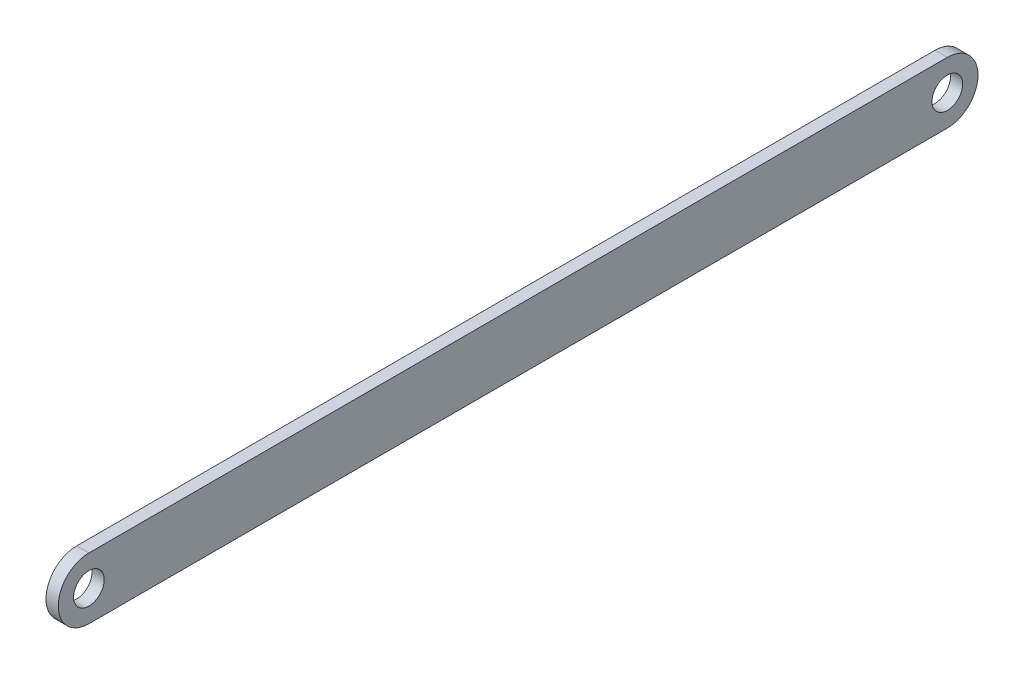
SolidWorks part; units mm, degrees
ref_plane "Front Plane" through (0, 0, 0) normal (0, 0, 1) x (1, 0, 0)
ref_plane "Top Plane" through (0, 0, 0) normal (0, 1, 0) x (1, 0, 0)
ref_plane "Right Plane" through (0, 0, 0) normal (1, 0, 0) x (0, 0, -1)
sketch "Sketch1" plane through (0, 0, 0) normal (1, 0, 0) x (0, 0, -1)
  line L0 (-70, 0) -> (70, 0) construction
  line L1 (-70, 5) -> (70, 5)
  line L2 (-70, -5) -> (70, -5)
  arc A0 (-70, 5) -> (-70, -5) centre (-70, 0) ccw
  arc A1 (70, -5) -> (70, 5) centre (70, 0) ccw
  circle A2 centre (-70, 0) radius 2.5
  circle A3 centre (70, 0) radius 2.5
  point P3 (0, 0)
  dimension "D3" = 5
  dimension "D1" = 140
  dimension "D2" = 10
extrude "Boss-Extrude1" add sketch "Sketch1" along normal mid plane 2
